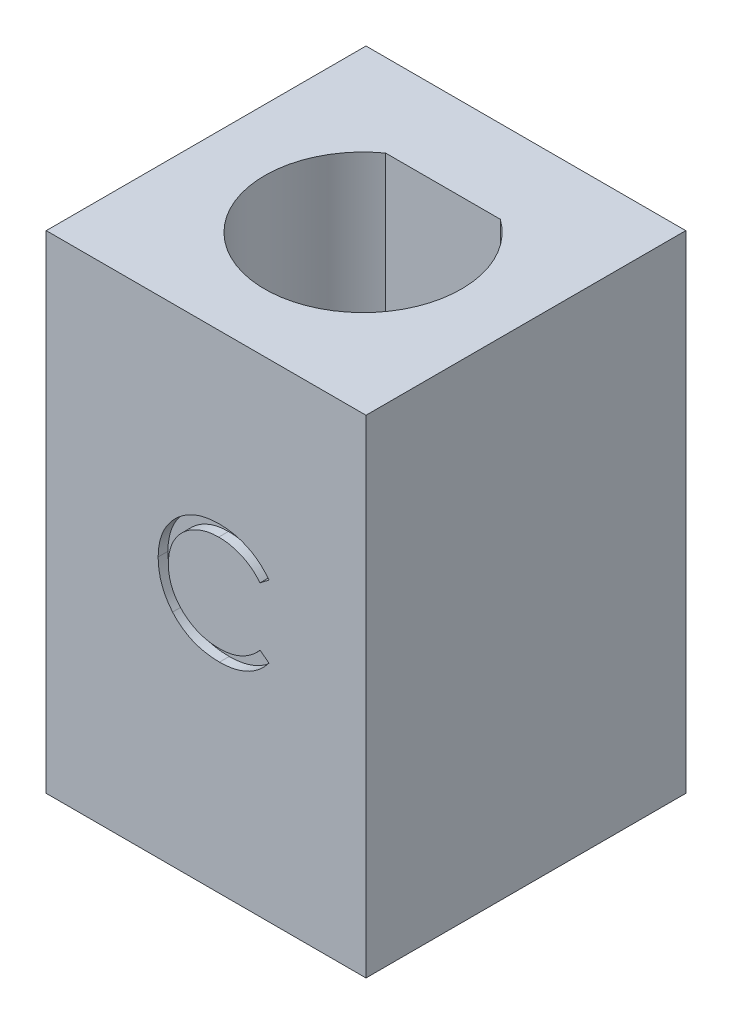
SolidWorks part; units mm, degrees
ref_plane "Front Plane" through (0, 0, 0) normal (0, 0, 1) x (1, 0, 0)
ref_plane "Top Plane" through (0, 0, 0) normal (0, 1, 0) x (1, 0, 0)
ref_plane "Right Plane" through (0, 0, 0) normal (1, 0, 0) x (0, 0, -1)
sketch "Sketch1" plane through (0, 0, 0) normal (0, 1, 0) x (1, 0, 0)
  line L0 (-1.765, 2.3694) -> (1.765, 2.3694)
  line L2 (-4.9207, 4.9207) -> (4.9207, 4.9207)
  line L3 (-4.9207, 4.9207) -> (-4.9207, -4.9207)
  line L4 (-4.9207, -4.9207) -> (4.9207, -4.9207)
  line L5 (4.9207, 4.9207) -> (4.9207, -4.9207)
  arc A1 (-1.765, 2.3694) -> (1.765, 2.3694) centre (0, -0.0906) ccw
  point P3 (0, 2.3694)
  dimension "D1" = 2.46
extrude "Boss-Extrude1" add sketch "Sketch1" along normal blind 15
sketch "Sketch2" plane through (0, 0, 4.9207) normal (0, 0, 1) x (1, 0, 0)
  text T0 "C"
extrude "Cut-Extrude1" cut sketch "Sketch2" against normal blind 0.3
